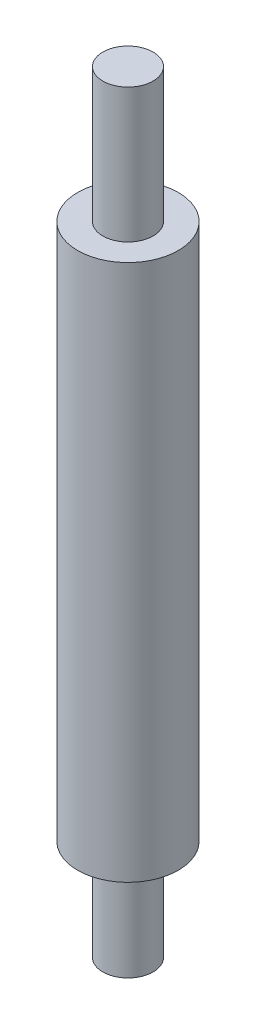
SolidWorks part; units mm, degrees
ref_plane "Front Plane" through (0, 0, 0) normal (0, 0, 1) x (1, 0, 0)
ref_plane "Top Plane" through (0, 0, 0) normal (0, 1, 0) x (1, 0, 0)
ref_plane "Right Plane" through (0, 0, 0) normal (1, 0, 0) x (0, 0, -1)
sketch "Sketch1" plane through (0, 0, 0) normal (0, 1, 0) x (1, 0, 0)
  circle A0 centre (0, 0) radius 1.5
  dimension "D1" = 3
extrude "Boss-Extrude1" add sketch "Sketch1" along normal blind 6
cosmetic thread "Cosmetic Thread2" parameters "D2"=2.439
sketch "Sketch2" plane through (0, 6, 0) normal (0, 1, 0) x (1, 0, 0)
  circle A0 centre (0, 0) radius 3
  dimension "D1" = 6
extrude "Boss-Extrude2" add sketch "Sketch2" along normal blind 32
sketch "Sketch3" plane through (0, 38, 0) normal (0, 1, 0) x (1, 0, 0)
  circle A0 centre (0, 0) radius 1.5
  dimension "D1" = 3
extrude "Boss-Extrude3" add sketch "Sketch3" along normal blind 8
cosmetic thread "Cosmetic Thread1" parameters "D2"=2.439
